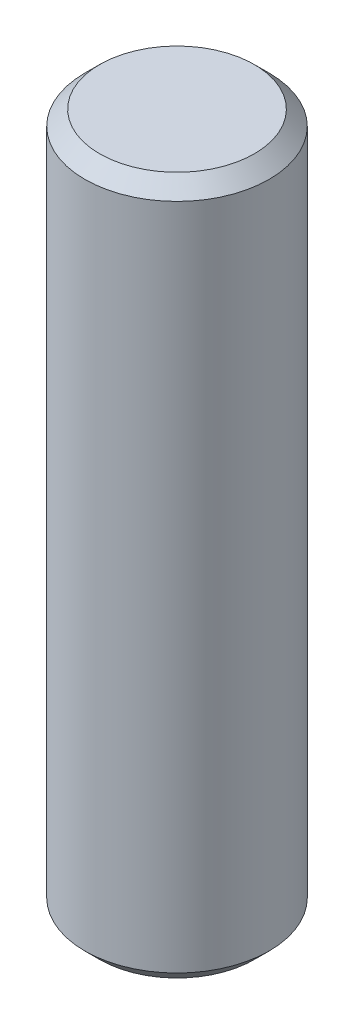
SolidWorks part; units mm, degrees
material "6061-T6 (SS)"
ref_plane "Front Plane" through (0, 0, 0) normal (0, 0, 1) x (1, 0, 0)
ref_plane "Top Plane" through (0, 0, 0) normal (0, 1, 0) x (1, 0, 0)
ref_plane "Right Plane" through (0, 0, 0) normal (1, 0, 0) x (0, 0, -1)
sketch "Sketch1" plane through (0, 0, 0) normal (0, 1, 0) x (1, 0, 0)
  circle A0 centre (0, 0) radius 3.1687
  dimension "D1" = 6.3373
extrude "Boss-Extrude1" add sketch "Sketch1" along normal blind 24
chamfer "Chamfer1" distance 0.508 angle 45 2 edges at (0, 24, 3.1687) (0, 0, 3.1687)
